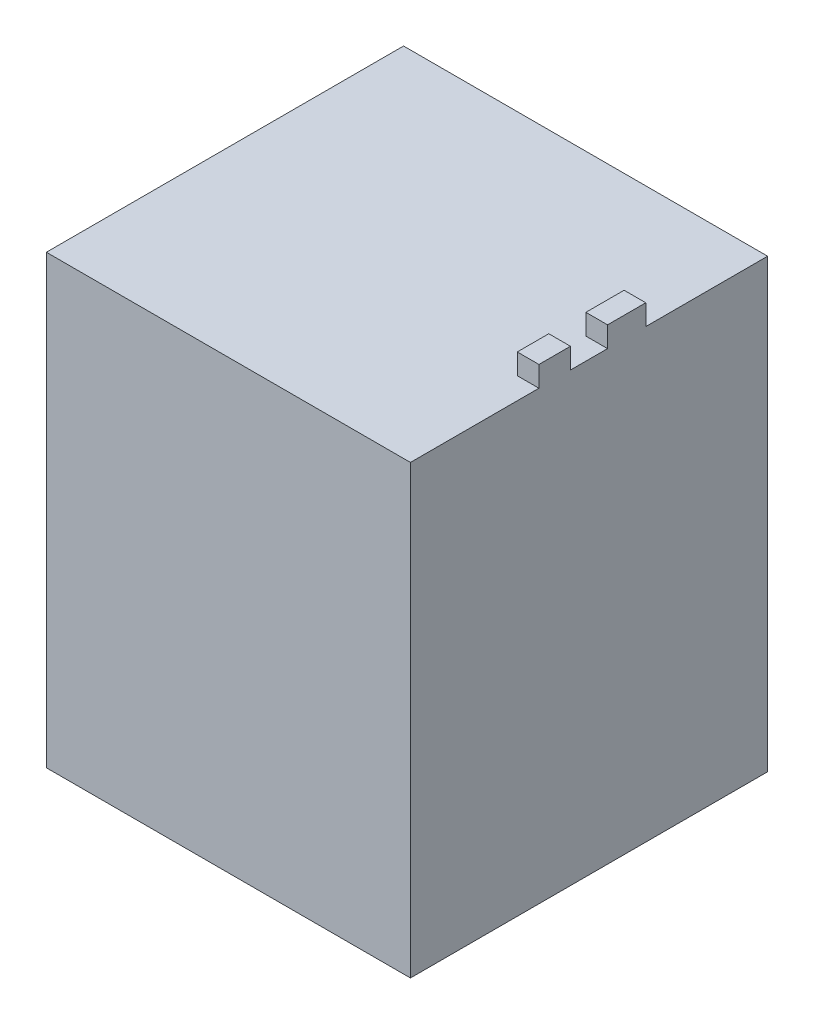
SolidWorks part; units mm, degrees
ref_plane "Front Plane" through (0, 0, 0) normal (0, 0, 1) x (1, 0, 0)
ref_plane "Top Plane" through (0, 0, 0) normal (0, 1, 0) x (1, 0, 0)
ref_plane "Right Plane" through (0, 0, 0) normal (1, 0, 0) x (0, 0, -1)
sketch "Sketch1" plane through (0, 0, 0) normal (0, 1, 0) x (1, 0, 0)
  line L1 (-12.4266, 38.8249) -> (40.5734, 38.8249)
  line L2 (-12.4266, 38.8249) -> (-12.4266, -13.1751)
  line L3 (-12.4266, -13.1751) -> (40.5734, -13.1751)
  line L4 (40.5734, 38.8249) -> (40.5734, -13.1751)
  dimension "D1" = 53
  dimension "D2" = 52
extrude "Boss-Extrude1" add sketch "Sketch1" along normal blind 65
ref_plane "Plane1" through (40.5734, 65, -38.8249) normal (-1, 0, 0) x (0, 0, 1)
sketch "Sketch3" plane through (0, 65, 0) normal (0, 1, 0) x (1, 0, 0)
  line L1 (40.5734, -13.1751) -> (40.5734, 38.8249) construction
  line L3 (40.5734, 21.0836) -> (37.4181, 21.0836)
  line L4 (40.5734, 21.0836) -> (40.5734, 15.5208)
  line L5 (40.5734, 15.5208) -> (37.4181, 15.5208)
  line L6 (37.4181, 21.0836) -> (37.4181, 15.5208)
  line L8 (40.5734, 10.1187) -> (37.4181, 10.1187)
  line L9 (40.5734, 10.1187) -> (40.5734, 5.5307)
  line L10 (40.5734, 5.5307) -> (37.4181, 5.5307)
  line L11 (37.4181, 10.1187) -> (37.4181, 5.5307)
extrude "Boss-Extrude2" add sketch "Sketch3" along normal blind 3
